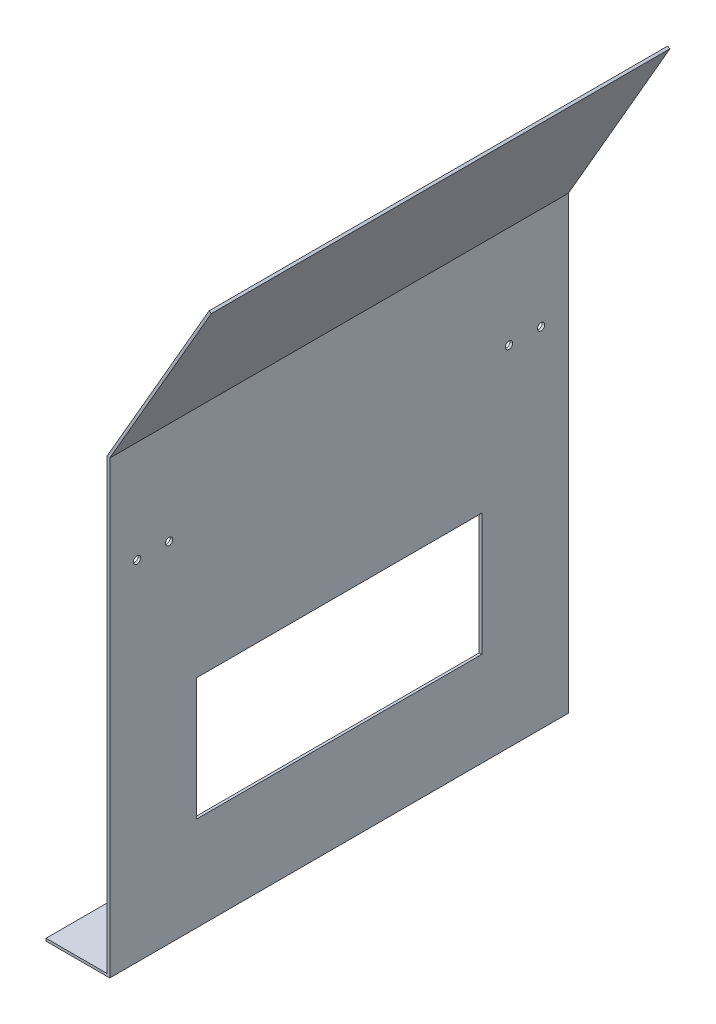
SolidWorks part; units mm, degrees
ref_plane "Front Plane" through (0, 0, 0) normal (0, 0, 1) x (1, 0, 0)
ref_plane "Top Plane" through (0, 0, 0) normal (0, 1, 0) x (1, 0, 0)
ref_plane "Right Plane" through (0, 0, 0) normal (1, 0, 0) x (0, 0, -1)
sketch "Sketch1" plane through (0, 0, 0) normal (0, 0, 1) x (1, 0, 0)
  line L0 (0, 0) -> (0, 279.4)
  line L1 (0, 279.4) -> (63.5, 389.3852)
  line L2 (1.6002, 0) -> (1.6002, 278.9712)
  line L3 (1.6002, 278.9712) -> (64.8858, 388.5851)
  line L4 (63.5, 389.3852) -> (64.8858, 388.5851)
  line L5 (1.6002, 0) -> (1.6002, -1.6002)
  line L6 (0, 0) -> (-38.1, 0)
  line L7 (0, -1.6002) -> (-38.1, -1.6002)
  line L8 (0, -1.6002) -> (1.6002, -1.6002)
  line L9 (-38.1, 0) -> (-38.1, -1.6002)
  dimension "D1" = 279.4
  dimension "D2" = 63.5
  dimension "D3" = 150
  dimension "D5" = 38.1
  dimension "D4" = 1.6002
  dimension "D6" = 1.6002
extrude "Boss-Extrude1" add sketch "Sketch1" along normal blind 285.75 contours L0 L1 L4 L3 L2 L5 L8 L7 L9 L6
sketch "Sketch2" plane through (1.6002, 0, 0) normal (1, 0, 0) x (0, 0, -1)
  line L0 (-142.875, 0) -> (-142.875, 95.25) construction
  line L1 (-231.775, 57.15) -> (-53.975, 57.15)
  line L2 (-231.775, 57.15) -> (-231.775, 133.35)
  line L3 (-231.775, 133.35) -> (-53.975, 133.35)
  line L4 (-53.975, 57.15) -> (-53.975, 133.35)
  line L5 (-231.775, 57.15) -> (-53.975, 133.35) construction
  line L6 (-231.775, 133.35) -> (-53.975, 57.15) construction
  line L9 (-285.75, 0) -> (0, 0) construction
  point P0 (-142.875, 95.25)
  dimension "D1" = 76.2
  dimension "D2" = 177.8
  dimension "D3" = 57.15
extrude "Cut-Extrude1" cut sketch "Sketch2" against normal through all
sketch "Sketch3" plane through (1.6002, 0, 0) normal (1, 0, 0) x (0, 0, -1)
  circle A0 centre (-268.7625, 215.4712) radius 2.2479
  circle A1 centre (-248.7625, 215.4712) radius 2.2479
  circle A2 centre (-16.9875, 215.4712) radius 2.2479
  circle A3 centre (-36.9875, 215.4712) radius 2.2479
  dimension "D1" = 4.4958
extrude "Cut-Extrude2" cut sketch "Sketch3" against normal up to next
